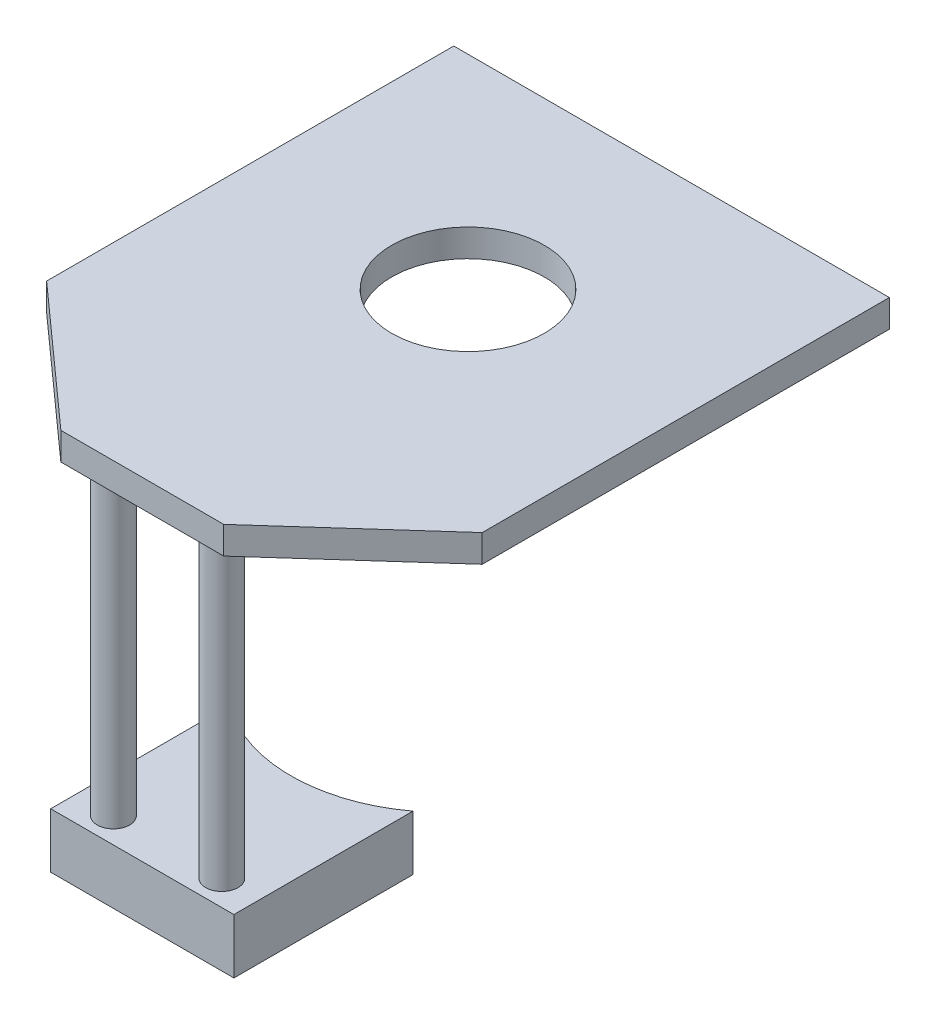
SolidWorks part; units mm, degrees
ref_plane "Front Plane" through (0, 0, 0) normal (0, 0, 1) x (1, 0, 0)
ref_plane "Top Plane" through (0, 0, 0) normal (0, 1, 0) x (1, 0, 0)
ref_plane "Right Plane" through (0, 0, 0) normal (1, 0, 0) x (0, 0, -1)
sketch "Sketch2" plane through (0, 0, 0) normal (0, 1, 0) x (1, 0, 0)
  line L0 (-107, -100) -> (-40, -160)
  line L1 (-107, 100) -> (107, 100)
  line L2 (-107, 100) -> (-107, -100)
  line L3 (-107, -100) -> (107, -100) construction
  line L4 (107, 100) -> (107, -100)
  line L5 (-107, 100) -> (107, -100) construction
  line L6 (-107, -100) -> (107, 100) construction
  line L7 (-40, -160) -> (40, -160)
  line L8 (40, -160) -> (107, -100)
  circle A0 centre (0, 0) radius 37.5
  point P0 (0, 0)
  dimension "D5" = 75
  dimension "D1" = 214
  dimension "D2" = 200
  dimension "D3" = 80
  dimension "D4" = 60
extrude "Boss-Extrude1" add sketch "Sketch2" along normal mid plane 13.5
sketch "Sketch3" plane through (0, -6.75, 0) normal (0, -1, 0) x (1, 0, 0)
  line L0 (-7.5431, 155.5) -> (69.4412, 155.5) construction
  line L1 (-40, 160) -> (40, 160) construction
  line L2 (-26.625, 147.55) -> (26.625, 147.55) construction
  circle A0 centre (26.625, 147.55) radius 7.95
  circle A1 centre (-26.625, 147.55) radius 7.95
  point P5 (26.625, 155.5)
  point P12 (0, 147.55)
  dimension "D1" = 4.5
  dimension "D2" = 15.9
  dimension "D3" = 53.25
extrude "Boss-Extrude2" add sketch "Sketch3" along normal blind 150
sketch "Sketch4" plane through (0, -156.75, 0) normal (0, -1, 0) x (1, 0, 0)
  line L0 (-40, 160) -> (40, 160) construction
  line L1 (-45, 72) -> (45, 72) construction
  line L2 (-45, 72) -> (-45, 160)
  line L3 (-45, 160) -> (45, 160)
  line L4 (45, 72) -> (45, 160)
  line L5 (-45, 72) -> (45, 160) construction
  line L6 (-45, 160) -> (45, 72) construction
  line L7 (-146.3734, 87) -> (146.3734, 87) construction
  arc A0 (45, 72) -> (-45, 72) centre (0, 12) ccw
  arc A1 (-45, 72) -> (45, 72) centre (0, 12) ccw construction
  point P0 (0, 116)
  point P13 (0, 87)
  dimension "D3" = 15
  dimension "D1" = 90
  dimension "D2" = 88
extrude "Boss-Extrude3" add sketch "Sketch4" along normal blind 27
equation "\"∩╗┐cas_w\" = 38.1mm"
equation "\"cas_l\" = 83.0mm"
equation "\"cas_h\" = 280.0mm"
equation "\"rail_w\" = 50.5mm"
equation "\"rail_c\" = 10.5mm"
equation "\"stinset_l\" = 160mm"
equation "\"stinset_w\" = 110mm"
equation "\"stinset_h\" = 3mm"
equation "\"stinset_fillet\" = 5mm"
equation "\"slide_l\" = 75.6mm"
equation "\"slide_w\" = 26mm"
equation "\"slide_h\" = 1.07mm"
equation "\"slide_fillet\" = 1mm"
equation "\"stxslide_l\" = 305mm"
equation "\"stxslide_w\" = 150mm"
equation "\"stxslide_h\" = 10mm"
equation "\"stmount_width\" = 214mm"
equation "\"D1@Sketch2\"=\"stmount_width\""
